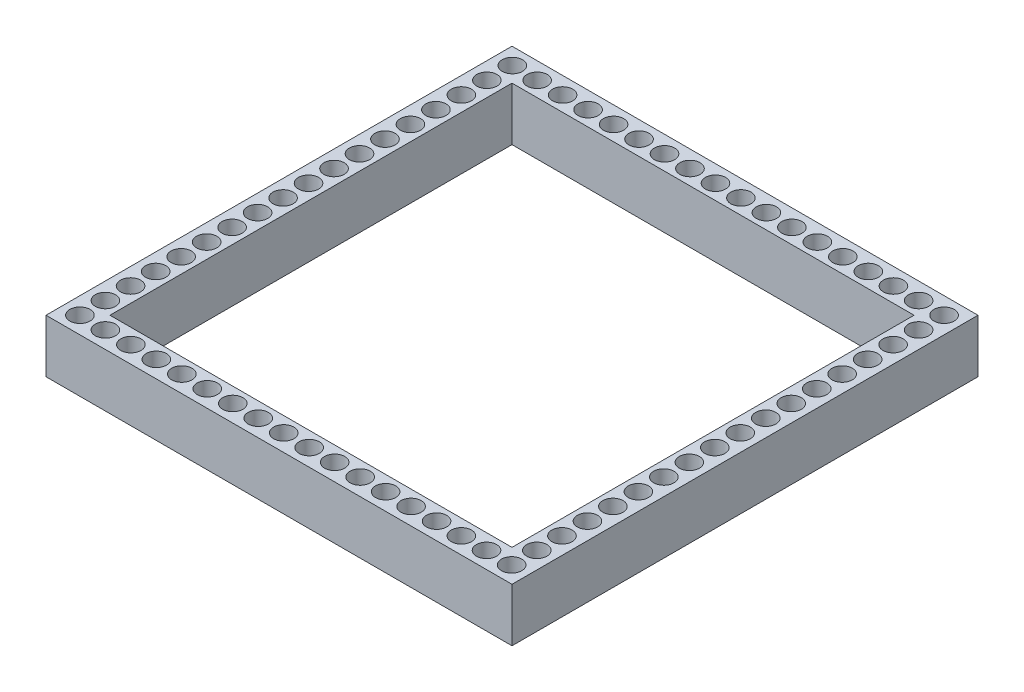
SolidWorks part; units mm, degrees
material "PP Copolymer"
ref_plane "Front Plane" through (0, 0, 0) normal (0, 0, 1) x (1, 0, 0)
ref_plane "Top Plane" through (0, 0, 0) normal (0, 1, 0) x (1, 0, 0)
ref_plane "Right Plane" through (0, 0, 0) normal (1, 0, 0) x (0, 0, -1)
sketch "Sketch2" plane through (0, 0, 0) normal (0, 1, 0) x (1, 0, 0)
  line L1 (-21.86, 21.86) -> (21.86, 21.86)
  line L2 (-21.86, 21.86) -> (-21.86, -21.86)
  line L3 (-21.86, -21.86) -> (21.86, -21.86)
  line L4 (21.86, 21.86) -> (21.86, -21.86)
  line L5 (-21.86, 21.86) -> (21.86, -21.86) construction
  line L6 (-21.86, -21.86) -> (21.86, 21.86) construction
  line L7 (-18.86, 18.86) -> (18.86, 18.86)
  line L8 (-18.86, 18.86) -> (-18.86, -18.86)
  line L9 (-18.86, -18.86) -> (18.86, -18.86)
  line L10 (18.86, 18.86) -> (18.86, -18.86)
  line L11 (-18.86, 18.86) -> (18.86, -18.86) construction
  line L12 (-18.86, -18.86) -> (18.86, 18.86) construction
  point P0 (0, 0)
  point P6 (0, 0)
  dimension "D1" = 43.72
  dimension "D2" = 43.72
  dimension "D3" = 37.72
  dimension "D4" = 37.72
extrude "Boss-Extrude1" add sketch "Sketch2" along normal blind 5
sketch "Sketch1" plane through (0, 0, 0) normal (0, 1, 0) x (1, 0, 0)
  circle A0 centre (-20.269, -20.269) radius 0.95
  circle A1 centre (-17.879, -20.269) radius 0.95
  circle A2 centre (-15.489, -20.269) radius 0.95
  circle A3 centre (-13.099, -20.269) radius 0.95
  circle A4 centre (-10.709, -20.269) radius 0.95
  circle A5 centre (-8.319, -20.269) radius 0.95
  circle A6 centre (-5.929, -20.269) radius 0.95
  circle A7 centre (-3.539, -20.269) radius 0.95
  circle A8 centre (-1.149, -20.269) radius 0.95
  circle A9 centre (1.241, -20.269) radius 0.95
  circle A10 centre (3.631, -20.269) radius 0.95
  circle A11 centre (6.021, -20.269) radius 0.95
  circle A12 centre (8.411, -20.269) radius 0.95
  circle A13 centre (10.801, -20.269) radius 0.95
  circle A14 centre (13.191, -20.269) radius 0.95
  circle A16 centre (20.269, 20.269) radius 0.95
  circle A17 centre (20.269, -15.581) radius 0.95
  circle A18 centre (20.269, -13.191) radius 0.95
  circle A19 centre (20.269, -10.801) radius 0.95
  circle A20 centre (20.269, -8.411) radius 0.95
  circle A21 centre (20.269, -6.021) radius 0.95
  circle A22 centre (20.269, -3.631) radius 0.95
  circle A23 centre (20.269, -1.241) radius 0.95
  circle A24 centre (20.269, 1.149) radius 0.95
  circle A25 centre (20.269, 3.539) radius 0.95
  circle A26 centre (20.269, 5.929) radius 0.95
  circle A27 centre (20.269, 8.319) radius 0.95
  circle A28 centre (20.269, 10.709) radius 0.95
  circle A29 centre (20.269, 13.099) radius 0.95
  circle A30 centre (20.269, 15.489) radius 0.95
  circle A31 centre (20.269, 17.879) radius 0.95
  circle A32 centre (13.159, 20.269) radius 0.95
  circle A33 centre (10.769, 20.269) radius 0.95
  circle A34 centre (8.379, 20.269) radius 0.95
  circle A35 centre (5.989, 20.269) radius 0.95
  circle A36 centre (3.599, 20.269) radius 0.95
  circle A37 centre (1.209, 20.269) radius 0.95
  circle A38 centre (-1.181, 20.269) radius 0.95
  circle A39 centre (-3.571, 20.269) radius 0.95
  circle A40 centre (-5.961, 20.269) radius 0.95
  circle A41 centre (-8.351, 20.269) radius 0.95
  circle A42 centre (-10.741, 20.269) radius 0.95
  circle A43 centre (-13.131, 20.269) radius 0.95
  circle A44 centre (-15.521, 20.269) radius 0.95
  circle A45 centre (-17.911, 20.269) radius 0.95
  circle A47 centre (-20.269, 20.301) radius 0.95
  circle A48 centre (-20.269, 17.911) radius 0.95
  circle A49 centre (-20.269, 15.521) radius 0.95
  circle A50 centre (-20.269, 13.131) radius 0.95
  circle A51 centre (-20.269, 10.741) radius 0.95
  circle A52 centre (-20.269, 8.351) radius 0.95
  circle A53 centre (-20.269, 5.961) radius 0.95
  circle A54 centre (-20.269, 3.571) radius 0.95
  circle A55 centre (-20.269, 1.181) radius 0.95
  circle A56 centre (-20.269, -1.209) radius 0.95
  circle A57 centre (-20.269, -3.599) radius 0.95
  circle A58 centre (-20.269, -5.989) radius 0.95
  circle A59 centre (-20.269, -8.379) radius 0.95
  circle A60 centre (-20.269, -10.769) radius 0.95
  circle A61 centre (-20.269, -13.159) radius 0.95
  circle A62 centre (15.581, -20.269) radius 0.95 [skipped]
  circle A63 centre (-20.269, -15.519) radius 0.95
  circle A64 centre (-20.269, -17.879) radius 0.95
  circle A65 centre (15.519, 20.269) radius 0.95
  circle A66 centre (17.879, 20.269) radius 0.95
  circle A67 centre (20.269, -17.941) radius 0.95
  circle A68 centre (20.269, -20.301) radius 0.95
  circle A69 centre (17.909, -20.301) radius 0.95
  circle A70 centre (15.549, -20.301) radius 0.95
  point P0 (-2.36, 2.36)
  dimension "D1" = 16
extrude "Cut-Extrude1" cut sketch "Sketch1" along normal through all
